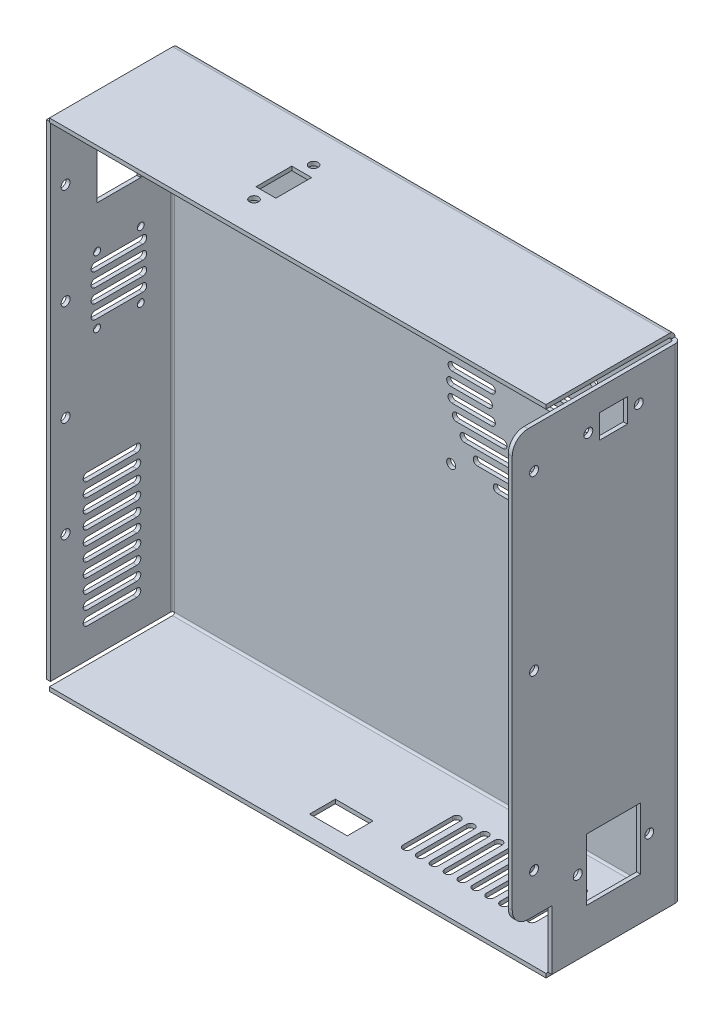
SolidWorks part; units mm, degrees
material "6061-T6 (SS)"
ref_plane "Front Plane" through (0, 0, 0) normal (0, 0, 1) x (1, 0, 0)
ref_plane "Top Plane" through (0, 0, 0) normal (0, 1, 0) x (1, 0, 0)
ref_plane "Right Plane" through (0, 0, 0) normal (1, 0, 0) x (0, 0, -1)
sketch "Sketch1" plane through (0, 0, 0) normal (0, 0, 1) x (1, 0, 0)
  line L0 (-128, 125) -> (128, -125) construction
  line L1 (-128, 125) -> (128, 125)
  line L2 (-128, 125) -> (-128, -125)
  line L3 (-128, -125) -> (128, -125)
  line L4 (128, 125) -> (128, -125)
  dimension "D1" = 256
  dimension "D2" = 250
extrude "Boss-Extrude1" add sketch "Sketch1" along normal blind 2
sketch "Sketch2" plane through (0, 0, 2) normal (0, 0, 1) x (1, 0, 0)
  line L1 (-128, 125) -> (128, 125)
  line L2 (-128, 125) -> (-128, -125)
  line L3 (-128, -125) -> (128, -125)
  line L4 (128, 125) -> (128, -125)
  line L5 (-126, 123) -> (126, 123)
  line L6 (-126, 123) -> (-126, -123)
  line L7 (-126, -123) -> (126, -123)
  line L8 (126, 123) -> (126, -123)
  dimension "D1" = 2
  dimension "D2" = 2
  dimension "D3" = 2
  dimension "D4" = 2
extrude "Boss-Extrude2" add sketch "Sketch2" along normal blind 63
fillet "Fillet1" radius 1 4 edges at (0, 123, 2) (126, 0, 2) (0, -123, 2) (-126, 0, 2)
fillet "Fillet2" radius 3 4 edges at (0, -125, 0) (128, 0, 0) (0, 125, 0) (-128, 0, 0)
sketch "Sketch3" plane through (0, 0, 65) normal (0, 0, 1) x (1, 0, 0)
  line L0 (-128, -125) -> (128, -125) construction
  line L1 (-125, 122) -> (-128, 122)
  line L2 (-125, 122) -> (-125, 125)
  line L3 (-125, 125) -> (-128, 125)
  line L4 (-128, 122) -> (-128, 125)
  line L5 (125, 122) -> (128, 122)
  line L6 (125, 122) -> (125, 125)
  line L7 (125, 125) -> (128, 125)
  line L8 (128, 122) -> (128, 125)
  line L9 (125, -122) -> (128, -122)
  line L10 (125, -122) -> (125, -125)
  line L11 (125, -125) -> (128, -125)
  line L12 (128, -122) -> (128, -125)
  line L13 (-125, -122) -> (-128, -122)
  line L14 (-125, -122) -> (-125, -125)
  line L15 (-125, -125) -> (-128, -125)
  line L16 (-128, -122) -> (-128, -125)
extrude "Cut-Extrude1" cut sketch "Sketch3" against normal through all
sketch "Sketch4" plane through (0, 0, 65) normal (0, 0, 1) x (1, 0, 0)
  line L0 (126, -122) -> (126, 122) construction
  line L1 (128, -122) -> (126, -122) construction
  line L4 (126, -122) -> (128, -122)
  line L5 (128, -122) -> (128, 122)
  line L6 (128, 122) -> (126, 122)
  line L7 (126, 122) -> (126, -122)
  line L8 (126, -92) -> (128, -92)
  line L9 (128, -92) -> (128, 122)
  line L10 (128, 122) -> (126, 122)
  line L11 (126, 122) -> (126, -92)
  dimension "D2" = 30
  dimension "D1" = 0
extrude "Boss-Extrude3" add sketch "Sketch4" along normal blind 20
sketch "Sketch5" plane through (-128, 0, 0) normal (-1, 0, 0) x (0, 0, 1)
  line L0 (18, 53.75) -> (40, 20.25) construction
  line L1 (18, 104) -> (40, 104)
  line L2 (18, 104) -> (18, 75)
  line L3 (18, 75) -> (40, 75)
  line L4 (40, 104) -> (40, 75)
  line L5 (17, 47.5) -> (41, 47.5) construction
  line L6 (20, -70) -> (45, -70) construction
  line L7 (20, -68) -> (45, -68)
  line L8 (20, -72) -> (45, -72)
  line L9 (20, -77) -> (45, -77) construction
  line L10 (20, -75) -> (45, -75)
  line L11 (20, -79) -> (45, -79)
  line L12 (20, -84) -> (45, -84) construction
  line L13 (20, -82) -> (45, -82)
  line L14 (20, -86) -> (45, -86)
  line L15 (20, -91) -> (45, -91) construction
  line L16 (20, -89) -> (45, -89)
  line L17 (20, -93) -> (45, -93)
  line L18 (20, -98) -> (45, -98) construction
  line L19 (20, -96) -> (45, -96)
  line L20 (20, -100) -> (45, -100)
  line L21 (20, -105) -> (45, -105) construction
  line L22 (20, -103) -> (45, -103)
  line L23 (20, -107) -> (45, -107)
  line L24 (32.5, -105) -> (32.5, -98) construction
  line L25 (32.5, -98) -> (32.5, -91) construction
  line L26 (32.5, -91) -> (32.5, -84) construction
  line L27 (32.5, -84) -> (32.5, -77) construction
  line L28 (32.5, -77) -> (32.5, -70) construction
  line L29 (3, -125) -> (65, -125) construction
  line L30 (65, 122) -> (65, -122) construction
  line L31 (65, -123) -> (3, -123) construction
  line L32 (0, -122) -> (0, 122) construction
  line L33 (20, -63) -> (45, -63) construction
  line L34 (20, -61) -> (45, -61)
  line L35 (20, -65) -> (45, -65)
  line L36 (20, -56) -> (45, -56) construction
  line L37 (20, -54) -> (45, -54)
  line L38 (20, -58) -> (45, -58)
  line L39 (20, -49) -> (45, -49) construction
  line L40 (20, -47) -> (45, -47)
  line L41 (20, -51) -> (45, -51)
  line L42 (20, -42) -> (45, -42) construction
  line L43 (20, -40) -> (45, -40)
  line L44 (20, -44) -> (45, -44)
  line L45 (32.5, -70) -> (32.5, -63) construction
  line L46 (32.5, -63) -> (32.5, -56) construction
  line L47 (32.5, -56) -> (32.5, -49) construction
  line L48 (32.5, -49) -> (32.5, -42) construction
  line L49 (29, 75) -> (29, 37) construction
  line L50 (17, 49.5) -> (41, 49.5)
  line L51 (17, 45.5) -> (41, 45.5)
  line L53 (17, 40.5) -> (41, 40.5) construction
  line L54 (17, 42.5) -> (41, 42.5)
  line L55 (17, 38.5) -> (41, 38.5)
  line L59 (17, 33.5) -> (41, 33.5) construction
  line L60 (17, 35.5) -> (41, 35.5)
  line L61 (17, 31.5) -> (41, 31.5)
  line L62 (17, 26.5) -> (41, 26.5) construction
  line L63 (17, 28.5) -> (41, 28.5)
  line L64 (17, 24.5) -> (41, 24.5)
  arc A0 (20, -68) -> (20, -72) centre (20, -70) ccw
  arc A1 (45, -72) -> (45, -68) centre (45, -70) ccw
  arc A2 (20, -75) -> (20, -79) centre (20, -77) ccw
  arc A3 (45, -79) -> (45, -75) centre (45, -77) ccw
  arc A4 (20, -82) -> (20, -86) centre (20, -84) ccw
  arc A5 (45, -86) -> (45, -82) centre (45, -84) ccw
  arc A6 (20, -89) -> (20, -93) centre (20, -91) ccw
  arc A7 (45, -93) -> (45, -89) centre (45, -91) ccw
  arc A8 (20, -96) -> (20, -100) centre (20, -98) ccw
  arc A9 (45, -100) -> (45, -96) centre (45, -98) ccw
  arc A10 (20, -103) -> (20, -107) centre (20, -105) ccw
  arc A11 (45, -107) -> (45, -103) centre (45, -105) ccw
  arc A12 (20, -61) -> (20, -65) centre (20, -63) ccw
  arc A13 (45, -65) -> (45, -61) centre (45, -63) ccw
  arc A14 (20, -54) -> (20, -58) centre (20, -56) ccw
  arc A15 (45, -58) -> (45, -54) centre (45, -56) ccw
  arc A16 (20, -47) -> (20, -51) centre (20, -49) ccw
  arc A17 (45, -51) -> (45, -47) centre (45, -49) ccw
  arc A18 (20, -40) -> (20, -44) centre (20, -42) ccw
  arc A19 (45, -44) -> (45, -40) centre (45, -42) ccw
  circle A20 centre (55.8527, 90.8) radius 2.25
  circle A21 centre (55.8527, 40) radius 2.25
  circle A22 centre (55.8527, -10.8) radius 2.25
  circle A23 centre (55.8527, -61.6) radius 2.25
  circle A24 centre (29, 37) radius 14.25 construction
  circle A25 centre (18, 53.75) radius 1.75
  circle A26 centre (40, 53.75) radius 1.75
  circle A27 centre (18, 20.25) radius 1.75
  circle A28 centre (40, 20.25) radius 1.75
  arc A29 (17, 49.5) -> (17, 45.5) centre (17, 47.5) ccw
  arc A30 (41, 45.5) -> (41, 49.5) centre (41, 47.5) ccw
  arc A31 (17, 42.5) -> (17, 38.5) centre (17, 40.5) ccw
  arc A32 (41, 38.5) -> (41, 42.5) centre (41, 40.5) ccw
  arc A35 (17, 35.5) -> (17, 31.5) centre (17, 33.5) ccw
  arc A36 (41, 31.5) -> (41, 35.5) centre (41, 33.5) ccw
  arc A37 (17, 28.5) -> (17, 24.5) centre (17, 26.5) ccw
  arc A38 (41, 24.5) -> (41, 28.5) centre (41, 26.5) ccw
  point P10 (32.5, -70)
  point P15 (32.5, -77)
  point P22 (32.5, -84)
  point P29 (32.5, -91)
  point P36 (32.5, -98)
  point P43 (32.5, -105)
  point P64 (32.5, -63)
  point P69 (32.5, -56)
  point P76 (32.5, -49)
  point P83 (32.5, -42)
  point P117 (29, 47.5)
  point P124 (29, 40.5)
  point P136 (29, 33.5)
  point P143 (29, 26.5)
  dimension "D8" = 2
  dimension "D9" = 4.5
  dimension "D13" = 28.5
  dimension "D17" = 3.5
  dimension "D16" = 3.5
  dimension "D21" = 2
  dimension "D2" = 22
  dimension "D3" = 200
  dimension "D4" = 20
  dimension "D5" = 7
  dimension "D6" = 20
  dimension "D7" = 20
  dimension "D10" = 40
  dimension "D11" = 29
  dimension "D12" = 33.5
  dimension "D14" = 22
  dimension "D15" = 160
  dimension "D18" = 3.5
  dimension "D19" = 24
  dimension "D20" = 7
  dimension "D22" = 7
extrude "Cut-Extrude2" cut sketch "Sketch5" against normal blind 15
sketch "Sketch6" plane through (128, 0, 0) normal (1, 0, 0) x (0, 0, -1)
  line L0 (-52, -85) -> (-47.65, -85) construction
  line L1 (-47.65, -69.45) -> (-20.35, -69.45)
  line L2 (-47.65, -69.45) -> (-47.65, -100.55)
  line L3 (-47.65, -100.55) -> (-20.35, -100.55)
  line L4 (-20.35, -69.45) -> (-20.35, -100.55)
  line L5 (-47.65, -85) -> (-20.35, -85) construction
  line L6 (-20.35, -85) -> (-16, -85) construction
  line L7 (-34, -100.55) -> (-34, -125) construction
  line L8 (-3, -125) -> (-65, -125) construction
  line L9 (-46.7, 105) -> (-41, 105) construction
  line L10 (-41, 111) -> (-27, 111)
  line L11 (-41, 111) -> (-41, 99)
  line L12 (-41, 99) -> (-27, 99)
  line L13 (-27, 111) -> (-27, 99)
  line L14 (-41, 105) -> (-27, 105) construction
  line L15 (-27, 105) -> (-21.3, 105) construction
  line L16 (-34, 99) -> (-34, -69.45) construction
  line L17 (-74, 102) -> (-74, 15) construction
  line L18 (-74, 15) -> (-74, -72) construction
  line L19 (-85, -92) -> (-85, 122) construction
  line L20 (-3, 122) -> (-85, 122) construction
  line L21 (-85, -92) -> (-65, -92) construction
  circle A0 centre (-16, -85) radius 2.25
  circle A1 centre (-52, -85) radius 2.25
  circle A2 centre (-46.7, 105) radius 2.25
  circle A3 centre (-21.3, 105) radius 2.25
  circle A4 centre (-74, -72) radius 2.25
  circle A5 centre (-74, 15) radius 2.25
  circle A6 centre (-74, 102) radius 2.25
  dimension "D3" = 4.5
  dimension "D10" = 4.5
  dimension "D1" = 27.3
  dimension "D2" = 36
  dimension "D4" = 31.1
  dimension "D5" = 40
  dimension "D6" = 14
  dimension "D7" = 12
  dimension "D8" = 25.4
  dimension "D9" = 230
  dimension "D11" = 11
  dimension "D12" = 20
  dimension "D13" = 20
extrude "Cut-Extrude3" cut sketch "Sketch6" against normal blind 15
fillet "Fillet3" radius 8 2 edges at (127, -92, 85) (127, 122, 85)
sketch "Sketch7" plane through (0, 125, 0) normal (0, 1, 0) x (1, 0, 0)
  line L0 (-128, -34) -> (-43, -34) construction
  line L1 (-43, -25) -> (-33, -25)
  line L2 (-43, -25) -> (-43, -43)
  line L3 (-43, -43) -> (-33, -43)
  line L4 (-33, -25) -> (-33, -43)
  line L5 (-128, -3) -> (-128, -65) construction
  line L6 (-38, -49) -> (-38, -43) construction
  line L7 (-38, -43) -> (-38, -25) construction
  line L8 (-38, -25) -> (-38, -19) construction
  circle A0 centre (-38, -19) radius 2.25
  circle A1 centre (-38, -49) radius 2.25
  dimension "D5" = 4.5
  dimension "D1" = 18
  dimension "D2" = 10
  dimension "D3" = 30
  dimension "D4" = 90
extrude "Cut-Extrude4" cut sketch "Sketch7" against normal blind 15
sketch "Sketch8" plane through (0, 0, 0) normal (0, 0, -1) x (-1, 0, 0)
  line L0 (-85.75, 83.75) -> (-14.25, 12.25) construction
  line L1 (-86, 48) -> (-67, 48) construction
  line L2 (-86, 50) -> (-67, 50)
  line L3 (-86, 46) -> (-67, 46)
  line L4 (-79.2404, 69) -> (-20.7596, 69) construction
  line L5 (-79.2404, 71) -> (-20.7596, 71)
  line L6 (-79.2404, 67) -> (-20.7596, 67)
  line L7 (-83.1662, 62) -> (-59.6437, 62) construction
  line L8 (-83.1662, 64) -> (-59.6437, 64)
  line L9 (-83.1662, 60) -> (-59.6437, 60)
  line L10 (-85.3129, 55) -> (-65.4919, 55) construction
  line L11 (-85.3129, 57) -> (-65.4919, 57)
  line L12 (-85.3129, 53) -> (-65.4919, 53)
  line L13 (-72.6274, 76) -> (-27.3726, 76) construction
  line L14 (-72.6274, 78) -> (-27.3726, 78)
  line L15 (-72.6274, 74) -> (-27.3726, 74)
  line L16 (-62.5, 83) -> (-37.5, 83) construction
  line L17 (-62.5, 85) -> (-37.5, 85)
  line L18 (-62.5, 81) -> (-37.5, 81)
  line L19 (-40.3563, 62) -> (-16.8338, 62) construction
  line L20 (-40.3563, 64) -> (-16.8338, 64)
  line L21 (-40.3563, 60) -> (-16.8338, 60)
  line L22 (-34.5081, 55) -> (-14.6871, 55) construction
  line L23 (-34.5081, 57) -> (-14.6871, 57)
  line L24 (-34.5081, 53) -> (-14.6871, 53)
  line L25 (-33, 48) -> (-14, 48) construction
  line L26 (-33, 50) -> (-14, 50)
  line L27 (-33, 46) -> (-14, 46)
  line L28 (-34.5081, 41) -> (-14.6871, 41) construction
  line L29 (-34.5081, 43) -> (-14.6871, 43)
  line L30 (-34.5081, 39) -> (-14.6871, 39)
  line L31 (-40.3563, 34) -> (-16.8338, 34) construction
  line L32 (-40.3563, 36) -> (-16.8338, 36)
  line L33 (-40.3563, 32) -> (-16.8338, 32)
  line L34 (-85.3129, 41) -> (-65.4919, 41) construction
  line L35 (-85.3129, 43) -> (-65.4919, 43)
  line L36 (-85.3129, 39) -> (-65.4919, 39)
  line L37 (-83.1662, 34) -> (-59.6437, 34) construction
  line L38 (-83.1662, 36) -> (-59.6437, 36)
  line L39 (-83.1662, 32) -> (-59.6437, 32)
  line L40 (-79.2404, 27) -> (-20.7596, 27) construction
  line L41 (-79.2404, 29) -> (-20.7596, 29)
  line L42 (-79.2404, 25) -> (-20.7596, 25)
  line L43 (-72.6274, 20) -> (-27.3726, 20) construction
  line L44 (-72.6274, 22) -> (-27.3726, 22)
  line L45 (-72.6274, 18) -> (-27.3726, 18)
  line L46 (-62.5, 13) -> (-37.5, 13) construction
  line L47 (-62.5, 15) -> (-37.5, 15)
  line L48 (-62.5, 11) -> (-37.5, 11)
  line L49 (-50, 13) -> (-50, 20) construction
  line L50 (-50, 20) -> (-50, 27) construction
  line L51 (-50, 27) -> (-50, 48) construction
  line L52 (-50, 48) -> (-50, 69) construction
  line L53 (-50, 69) -> (-50, 76) construction
  line L54 (-50, 76) -> (-50, 83) construction
  line L55 (-20.7596, 62) -> (-20.7596, 55) construction
  line L56 (-20.7596, 55) -> (-20.7596, 48) construction
  line L57 (-20.7596, 48) -> (-20.7596, 41) construction
  line L58 (-20.7596, 41) -> (-20.7596, 34) construction
  line L59 (-29.6435, 69) -> (-29.6435, 62) construction
  line L60 (-27.3726, 34) -> (-27.3726, 27) construction
  circle A0 centre (-85.75, 83.75) radius 2.25
  circle A1 centre (-85.75, 12.25) radius 2.25
  circle A2 centre (-14.25, 83.75) radius 2.25
  circle A3 centre (-14.25, 12.25) radius 2.25
  circle A4 centre (-50, 48) radius 15 construction
  circle A5 centre (-50, 48) radius 38 construction
  arc A6 (-86, 50) -> (-86, 46) centre (-86, 48) ccw
  arc A7 (-67, 46) -> (-67, 50) centre (-67, 48) ccw
  arc A8 (-79.2404, 71) -> (-79.2404, 67) centre (-79.2404, 69) ccw
  arc A9 (-20.7596, 67) -> (-20.7596, 71) centre (-20.7596, 69) ccw
  arc A10 (-83.1662, 64) -> (-83.1662, 60) centre (-83.1662, 62) ccw
  arc A11 (-59.6437, 60) -> (-59.6437, 64) centre (-59.6437, 62) ccw
  arc A12 (-85.3129, 57) -> (-85.3129, 53) centre (-85.3129, 55) ccw
  arc A13 (-65.4919, 53) -> (-65.4919, 57) centre (-65.4919, 55) ccw
  arc A14 (-72.6274, 78) -> (-72.6274, 74) centre (-72.6274, 76) ccw
  arc A15 (-27.3726, 74) -> (-27.3726, 78) centre (-27.3726, 76) ccw
  arc A16 (-62.5, 85) -> (-62.5, 81) centre (-62.5, 83) ccw
  arc A17 (-37.5, 81) -> (-37.5, 85) centre (-37.5, 83) ccw
  arc A18 (-40.3563, 64) -> (-40.3563, 60) centre (-40.3563, 62) ccw
  arc A19 (-16.8338, 60) -> (-16.8338, 64) centre (-16.8338, 62) ccw
  arc A20 (-34.5081, 57) -> (-34.5081, 53) centre (-34.5081, 55) ccw
  arc A21 (-14.6871, 53) -> (-14.6871, 57) centre (-14.6871, 55) ccw
  arc A22 (-33, 50) -> (-33, 46) centre (-33, 48) ccw
  arc A23 (-14, 46) -> (-14, 50) centre (-14, 48) ccw
  arc A24 (-34.5081, 43) -> (-34.5081, 39) centre (-34.5081, 41) ccw
  arc A25 (-14.6871, 39) -> (-14.6871, 43) centre (-14.6871, 41) ccw
  arc A26 (-40.3563, 36) -> (-40.3563, 32) centre (-40.3563, 34) ccw
  arc A27 (-16.8338, 32) -> (-16.8338, 36) centre (-16.8338, 34) ccw
  arc A28 (-85.3129, 43) -> (-85.3129, 39) centre (-85.3129, 41) ccw
  arc A29 (-65.4919, 39) -> (-65.4919, 43) centre (-65.4919, 41) ccw
  arc A30 (-83.1662, 36) -> (-83.1662, 32) centre (-83.1662, 34) ccw
  arc A31 (-59.6437, 32) -> (-59.6437, 36) centre (-59.6437, 34) ccw
  arc A32 (-79.2404, 29) -> (-79.2404, 25) centre (-79.2404, 27) ccw
  arc A33 (-20.7596, 25) -> (-20.7596, 29) centre (-20.7596, 27) ccw
  arc A34 (-72.6274, 22) -> (-72.6274, 18) centre (-72.6274, 20) ccw
  arc A35 (-27.3726, 18) -> (-27.3726, 22) centre (-27.3726, 20) ccw
  arc A36 (-62.5, 15) -> (-62.5, 11) centre (-62.5, 13) ccw
  arc A37 (-37.5, 11) -> (-37.5, 15) centre (-37.5, 13) ccw
  point P17 (-76.5, 48)
  point P22 (-50, 69)
  point P29 (-71.4049, 62)
  point P36 (-75.4024, 55)
  point P43 (-50, 76)
  point P50 (-50, 83)
  point P57 (-28.5951, 62)
  point P64 (-24.5976, 55)
  point P71 (-23.5, 48)
  point P78 (-24.5976, 41)
  point P85 (-28.5951, 34)
  point P92 (-75.4024, 41)
  point P99 (-71.4049, 34)
  point P106 (-50, 27)
  point P113 (-50, 20)
  point P120 (-50, 13)
  dimension "D1" = 4.5
  dimension "D2" = 30
  dimension "D3" = 76
  dimension "D5" = 2
  dimension "D4" = 7
  dimension "D6" = 25
extrude "Cut-Extrude5" cut sketch "Sketch8" against normal blind 15
sketch "Sketch9" plane through (0, -125, 0) normal (0, -1, 0) x (1, 0, 0)
  line L0 (42, 45) -> (42, 20) construction
  line L1 (44, 45) -> (44, 20)
  line L2 (40, 45) -> (40, 20)
  line L3 (49, 45) -> (49, 20) construction
  line L4 (51, 45) -> (51, 20)
  line L5 (47, 45) -> (47, 20)
  line L6 (56, 45) -> (56, 20) construction
  line L7 (58, 45) -> (58, 20)
  line L8 (54, 45) -> (54, 20)
  line L9 (63, 45) -> (63, 20) construction
  line L10 (65, 45) -> (65, 20)
  line L11 (61, 45) -> (61, 20)
  line L12 (70, 45) -> (70, 20) construction
  line L13 (72, 45) -> (72, 20)
  line L14 (68, 45) -> (68, 20)
  line L15 (77, 45) -> (77, 20) construction
  line L16 (79, 45) -> (79, 20)
  line L17 (75, 45) -> (75, 20)
  line L18 (84, 45) -> (84, 20) construction
  line L19 (86, 45) -> (86, 20)
  line L20 (82, 45) -> (82, 20)
  line L21 (91, 45) -> (91, 20) construction
  line L22 (93, 45) -> (93, 20)
  line L23 (89, 45) -> (89, 20)
  line L24 (98, 45) -> (98, 20) construction
  line L25 (100, 45) -> (100, 20)
  line L26 (96, 45) -> (96, 20)
  line L27 (35, 45) -> (35, 20) construction
  line L28 (37, 45) -> (37, 20)
  line L29 (33, 45) -> (33, 20)
  line L30 (128, 3) -> (128, 65) construction
  line L31 (-2, 53.05) -> (-2, 44.05) construction
  line L32 (35, 32.5) -> (42, 32.5) construction
  line L33 (42, 32.5) -> (49, 32.5) construction
  line L34 (49, 32.5) -> (56, 32.5) construction
  line L35 (56, 32.5) -> (63, 32.5) construction
  line L36 (63, 32.5) -> (70, 32.5) construction
  line L37 (70, 32.5) -> (77, 32.5) construction
  line L38 (77, 32.5) -> (84, 32.5) construction
  line L39 (84, 32.5) -> (91, 32.5) construction
  line L40 (91, 32.5) -> (98, 32.5) construction
  line L41 (-4, 55.05) -> (15, 55.05)
  line L42 (125, 0) -> (-125, 0) construction
  line L43 (-125, 65) -> (125, 65) construction
  line L44 (-4, 55.05) -> (-4, 42.05)
  line L45 (-4, 42.05) -> (15, 42.05)
  line L46 (15, 55.05) -> (15, 42.05)
  line L47 (-2, 44.05) -> (13, 44.05) construction
  line L48 (13, 44.05) -> (13, 53.05) construction
  line L49 (13, 53.05) -> (-2, 53.05) construction
  arc A0 (44, 45) -> (40, 45) centre (42, 45) ccw
  arc A1 (40, 20) -> (44, 20) centre (42, 20) ccw
  arc A2 (51, 45) -> (47, 45) centre (49, 45) ccw
  arc A3 (47, 20) -> (51, 20) centre (49, 20) ccw
  arc A4 (58, 45) -> (54, 45) centre (56, 45) ccw
  arc A5 (54, 20) -> (58, 20) centre (56, 20) ccw
  arc A6 (65, 45) -> (61, 45) centre (63, 45) ccw
  arc A7 (61, 20) -> (65, 20) centre (63, 20) ccw
  arc A8 (72, 45) -> (68, 45) centre (70, 45) ccw
  arc A9 (68, 20) -> (72, 20) centre (70, 20) ccw
  arc A10 (79, 45) -> (75, 45) centre (77, 45) ccw
  arc A11 (75, 20) -> (79, 20) centre (77, 20) ccw
  arc A12 (86, 45) -> (82, 45) centre (84, 45) ccw
  arc A13 (82, 20) -> (86, 20) centre (84, 20) ccw
  arc A14 (93, 45) -> (89, 45) centre (91, 45) ccw
  arc A15 (89, 20) -> (93, 20) centre (91, 20) ccw
  arc A16 (100, 45) -> (96, 45) centre (98, 45) ccw
  arc A17 (96, 20) -> (100, 20) centre (98, 20) ccw
  arc A18 (37, 45) -> (33, 45) centre (35, 45) ccw
  arc A19 (33, 20) -> (37, 20) centre (35, 20) ccw
  point P2 (42, 32.5)
  point P7 (49, 32.5)
  point P14 (56, 32.5)
  point P21 (63, 32.5)
  point P28 (70, 32.5)
  point P35 (77, 32.5)
  point P42 (84, 32.5)
  point P49 (91, 32.5)
  point P56 (98, 32.5)
  point P63 (35, 32.5)
  dimension "D2" = 2
  dimension "D1" = 20
  dimension "D3" = 7
  dimension "D4" = 20
  dimension "D5" = 30
  dimension "D6" = 2
  dimension "D7" = 2
  dimension "D8" = 2
  dimension "D9" = 2
extrude "Cut-Extrude6" cut sketch "Sketch9" against normal blind 15
sketch "Sketch10" plane through (0, 0, 65) normal (0, 0, 1) x (1, 0, 0)
  line L4 (-128, -122) -> (-126, -122)
  line L5 (-126, -122) -> (-126, 122)
  line L6 (-126, 122) -> (-128, 122)
  line L7 (-128, 122) -> (-128, -122)
  line L8 (-128, -122) -> (-126, -122)
  line L9 (-126, -122) -> (-126, 122)
  line L10 (-126, 122) -> (-128, 122)
  line L11 (-128, 122) -> (-128, -122)
  dimension "D1" = 0
extrude "Cut-Extrude7" cut sketch "Sketch10" against normal blind 1.5
